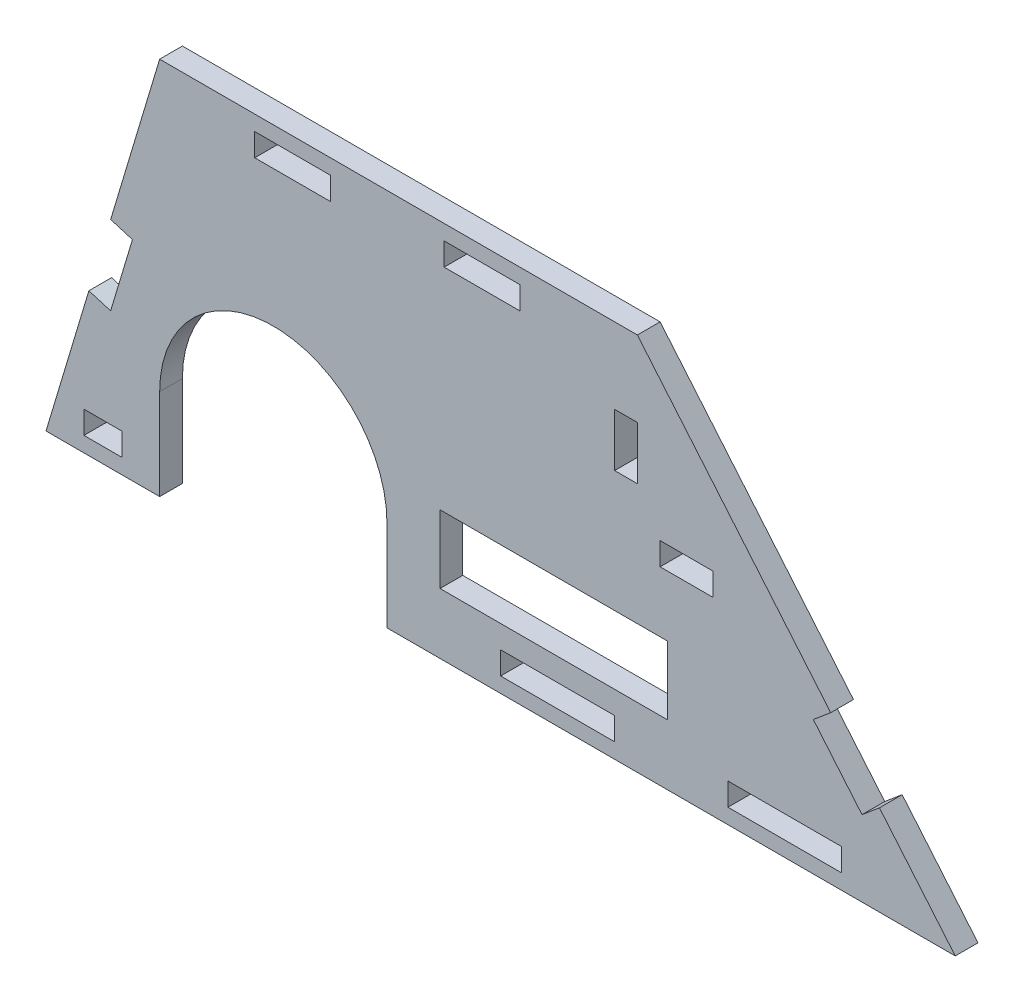
SolidWorks part; units mm, degrees
ref_plane "Alzado" through (0, 0, 0) normal (0, 0, 1) x (1, 0, 0)
ref_plane "Planta" through (0, 0, 0) normal (0, 1, 0) x (1, 0, 0)
ref_plane "Vista lateral" through (0, 0, 0) normal (1, 0, 0) x (0, 0, -1)
sketch "Croquis1" plane through (0, 0, 0) normal (0, 0, 1) x (1, 0, 0)
  line L0 (0, 0) -> (15, 0)
  line L1 (120, 0) -> (78.045, 50)
  line L2 (78.045, 50) -> (15, 50)
  line L3 (15, 50) -> (0, 0)
  line L4 (15, 0) -> (15, 12)
  line L5 (45, 0) -> (45, 12)
  line L6 (45, 0) -> (120, 0)
  line L8 (105, 5) -> (90, 5)
  line L9 (105, 5) -> (105, 2)
  line L10 (105, 2) -> (90, 2)
  line L11 (90, 5) -> (90, 2)
  line L12 (105, 5) -> (90, 2) construction
  line L13 (105, 2) -> (90, 5) construction
  line L14 (75, 5) -> (60, 5)
  line L15 (75, 5) -> (75, 2)
  line L16 (75, 2) -> (60, 2)
  line L17 (60, 5) -> (60, 2)
  line L18 (75, 5) -> (60, 2) construction
  line L19 (75, 2) -> (60, 5) construction
  line L20 (10, 2) -> (5, 2)
  line L21 (10, 2) -> (10, 5)
  line L22 (10, 5) -> (5, 5)
  line L23 (5, 2) -> (5, 5)
  line L24 (10, 2) -> (5, 5) construction
  line L25 (10, 5) -> (5, 2) construction
  line L26 (82, 8) -> (52, 8)
  line L27 (82, 8) -> (82, 17)
  line L28 (82, 17) -> (52, 17)
  line L29 (52, 8) -> (52, 17)
  line L30 (82, 8) -> (52, 17) construction
  line L31 (82, 17) -> (52, 8) construction
  arc A0 (45, 12) -> (15, 12) centre (30, 12) ccw
  point P6 (97.5, 3.5)
  point P11 (67.5, 3.5)
  point P20 (7.5, 3.5)
  point P25 (67, 12.5)
  dimension "D5" = 30
  dimension "D1" = 120
  dimension "D2" = 50
  dimension "D3" = 50
  dimension "D4" = 15
  dimension "D6" = 5
  dimension "D7" = 12
  dimension "D8" = 15
  dimension "D9" = 3
  dimension "D10" = 15
  dimension "D11" = 15
  dimension "D12" = 3
  dimension "D13" = 15
  dimension "D14" = 2
  dimension "D15" = 5
  dimension "D16" = 3
  dimension "D17" = 2
  dimension "D19" = 8
  dimension "D20" = 30
  dimension "D21" = 9
  dimension "D22" = 7
extrude "Saliente-Extruir1" add sketch "Croquis1" along normal blind 3
sketch "Croquis3" plane through (0, 0, 3) normal (0, 0, 1) x (1, 0, 0)
  line L6 (78.045, 50) -> (78.045, 13.6274) construction
  line L15 (78.045, 33) -> (75.045, 33)
  line L16 (78.045, 33) -> (78.045, 40)
  line L17 (78.045, 40) -> (75.045, 40)
  line L18 (75.045, 33) -> (75.045, 40)
  line L19 (78.045, 33) -> (75.045, 40) construction
  line L20 (78.045, 40) -> (75.045, 33) construction
  line L22 (78.045, 50) -> (15, 50) construction
  line L23 (88.045, 25) -> (81.045, 25)
  line L24 (88.045, 25) -> (88.045, 28)
  line L25 (88.045, 28) -> (81.045, 28)
  line L26 (81.045, 25) -> (81.045, 28)
  line L27 (88.045, 25) -> (81.045, 28) construction
  line L28 (88.045, 28) -> (81.045, 25) construction
  point P0 (76.545, 36.5)
  point P11 (84.545, 26.5)
  dimension "D1" = 3
  dimension "D2" = 7
  dimension "D3" = 3
  dimension "D4" = 7
  dimension "D5" = 5
  dimension "D6" = 3
  dimension "D7" = 10
extrude "Cortar-Extruir2" cut sketch "Croquis3" against normal through all
sketch "Croquis5" plane through (0, 0, 3) normal (0, 0, 1) x (1, 0, 0)
  line L0 (103.563, 19.5888) -> (101.2649, 17.6604)
  line L1 (120, 0) -> (78.045, 50) construction
  line L2 (101.2649, 17.6604) -> (107.6928, 10)
  line L3 (107.6928, 10) -> (109.9909, 11.9284)
  line L4 (45, 0) -> (120, 0) construction
  line L5 (103.563, 19.5888) -> (109.9909, 11.9284)
  dimension "D1" = 3
  dimension "D2" = 10
  dimension "D3" = 10
extrude "Cortar-Extruir3" cut sketch "Croquis5" against normal through all
sketch "Croquis6" plane through (0, 0, 3) normal (0, 0, 1) x (1, 0, 0)
  line L0 (8.5321, 28.4403) -> (11.4056, 27.5783)
  line L1 (15, 50) -> (0, 0) construction
  line L2 (11.4056, 27.5783) -> (8.5321, 18)
  line L3 (8.5321, 18) -> (5.6586, 18.862)
  line L4 (0, 0) -> (15, 0) construction
  line L5 (8.5321, 28.4403) -> (5.6586, 18.862)
  dimension "D1" = 3
  dimension "D2" = 10
  dimension "D3" = 18
extrude "Cortar-Extruir4" cut sketch "Croquis6" against normal through all
sketch "Croquis7" plane through (0, 0, 0) normal (0, 0, -1) x (-1, 0, 0)
  line L0 (-78.045, 50) -> (-15, 50) construction
  line L1 (-52.545, 48) -> (-62.545, 48)
  line L2 (-52.545, 48) -> (-52.545, 45)
  line L3 (-52.545, 45) -> (-62.545, 45)
  line L4 (-62.545, 48) -> (-62.545, 45)
  line L5 (-52.545, 48) -> (-62.545, 45) construction
  line L6 (-52.545, 45) -> (-62.545, 48) construction
  line L7 (-37.545, 45) -> (-27.545, 45)
  line L8 (-37.545, 45) -> (-37.545, 48)
  line L9 (-37.545, 48) -> (-27.545, 48)
  line L10 (-27.545, 45) -> (-27.545, 48)
  line L11 (-37.545, 45) -> (-27.545, 48) construction
  line L12 (-37.545, 48) -> (-27.545, 45) construction
  point P0 (-57.545, 46.5)
  point P5 (-32.545, 46.5)
  dimension "D1" = 10
  dimension "D2" = 3
  dimension "D3" = 3
  dimension "D4" = 10
  dimension "D5" = 15.5
  dimension "D6" = 15
  dimension "D7" = 2
  dimension "D8" = 2
extrude "Cortar-Extruir5" cut sketch "Croquis7" against normal through all
